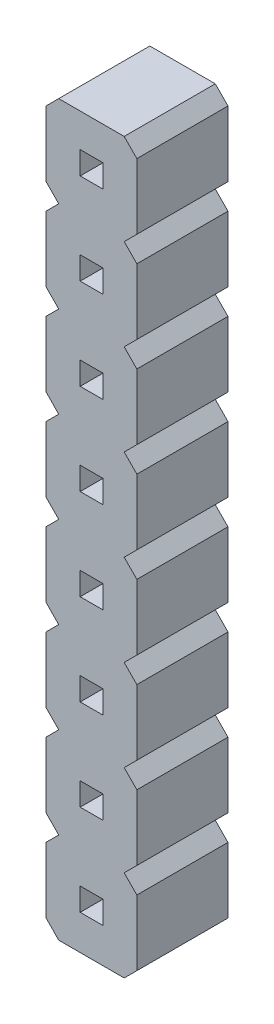
SolidWorks part; units mm, degrees
ref_plane "Alzado" through (0, 0, 0) normal (0, 0, 1) x (1, 0, 0)
ref_plane "Planta" through (0, 0, 0) normal (0, 1, 0) x (1, 0, 0)
ref_plane "Vista lateral" through (0, 0, 0) normal (1, 0, 0) x (0, 0, -1)
sketch "pin_drawing" plane through (0, 0, 0) normal (0, 0, 1) x (1, 0, 0)
  line L0 (0.9381, -1.0393) -> (-0.0144, -1.0393) construction
  line L1 (-0.0144, 2.0791) -> (-0.0144, 0.2531)
  line L2 (-0.0144, -0.4609) -> (-0.0144, -2.2869)
  line L3 (-0.0144, -0.4609) -> (0.3392, -0.1073)
  line L4 (1.5741, -1.6753) -> (2.5183, -1.6753) construction
  line L5 (-0.0144, 2.0791) -> (0.3392, 2.4327)
  line L6 (2.5183, -0.4665) -> (2.5183, -2.2938)
  line L7 (0.9381, -1.3573) -> (0.9381, -1.0393) construction
  line L8 (2.5183, -2.2938) -> (2.1647, -2.6473)
  line L9 (2.1647, -0.1073) -> (2.5183, -0.4665)
  line L10 (1.5741, -1.3573) -> (1.5741, -1.6753) construction
  line L11 (0.3392, -2.6473) -> (-0.0144, -2.2869)
  line L12 (0.9381, -1.0393) -> (1.5741, -1.0393)
  line L13 (0.9381, -1.0393) -> (0.9381, -1.6753)
  line L14 (0.9381, -1.6753) -> (1.5741, -1.6753)
  line L15 (1.5741, -1.0393) -> (1.5741, -1.6753)
  line L16 (2.5183, 2.0735) -> (2.5183, 0.2462)
  line L17 (2.5183, 0.2462) -> (2.1647, -0.1073)
  line L18 (2.1647, 2.4327) -> (2.5183, 2.0735)
  line L19 (0.3392, -0.1073) -> (-0.0144, 0.2531)
  line L20 (0.9381, 1.5007) -> (1.5741, 1.5007)
  line L21 (0.9381, 1.5007) -> (0.9381, 0.8647)
  line L22 (0.9381, 0.8647) -> (1.5741, 0.8647)
  line L23 (1.5741, 1.5007) -> (1.5741, 0.8647)
  line L24 (0.9381, 1.5007) -> (-0.0144, 1.5007) construction
  line L25 (1.5741, 0.8647) -> (2.5183, 0.8647) construction
  line L26 (0.9381, 1.1827) -> (0.9381, 1.5007) construction
  line L27 (1.5741, 1.1827) -> (1.5741, 0.8647) construction
  line L28 (-0.0144, 4.6191) -> (-0.0144, 2.7931)
  line L29 (-0.0144, 4.6191) -> (0.3392, 4.9727)
  line L30 (2.5183, 4.6135) -> (2.5183, 2.7862)
  line L31 (2.5183, 2.7862) -> (2.1647, 2.4327)
  line L32 (2.1647, 4.9727) -> (2.5183, 4.6135)
  line L33 (0.3392, 2.4327) -> (-0.0144, 2.7931)
  line L34 (0.9381, 4.0407) -> (1.5741, 4.0407)
  line L35 (0.9381, 4.0407) -> (0.9381, 3.4047)
  line L36 (0.9381, 3.4047) -> (1.5741, 3.4047)
  line L37 (1.5741, 4.0407) -> (1.5741, 3.4047)
  line L38 (0.9381, 4.0407) -> (-0.0144, 4.0407) construction
  line L39 (1.5741, 3.4047) -> (2.5183, 3.4047) construction
  line L40 (0.9381, 3.7227) -> (0.9381, 4.0407) construction
  line L41 (1.5741, 3.7227) -> (1.5741, 3.4047) construction
  line L42 (-0.0144, 7.1591) -> (-0.0144, 5.3331)
  line L43 (-0.0144, 7.1591) -> (0.3392, 7.5127)
  line L44 (2.5183, 7.1535) -> (2.5183, 5.3262)
  line L45 (2.5183, 5.3262) -> (2.1647, 4.9727)
  line L46 (2.1647, 7.5127) -> (2.5183, 7.1535)
  line L47 (0.3392, 4.9727) -> (-0.0144, 5.3331)
  line L48 (0.9381, 6.5807) -> (1.5741, 6.5807)
  line L49 (0.9381, 6.5807) -> (0.9381, 5.9447)
  line L50 (0.9381, 5.9447) -> (1.5741, 5.9447)
  line L51 (1.5741, 6.5807) -> (1.5741, 5.9447)
  line L52 (0.9381, 6.5807) -> (-0.0144, 6.5807) construction
  line L53 (1.5741, 5.9447) -> (2.5183, 5.9447) construction
  line L54 (0.9381, 6.2627) -> (0.9381, 6.5807) construction
  line L55 (1.5741, 6.2627) -> (1.5741, 5.9447) construction
  line L56 (-0.0144, 9.6991) -> (-0.0144, 7.8731)
  line L57 (-0.0144, 9.6991) -> (0.3392, 10.0527)
  line L58 (2.5183, 9.6935) -> (2.5183, 7.8662)
  line L59 (2.5183, 7.8662) -> (2.1647, 7.5127)
  line L60 (2.1647, 10.0527) -> (2.5183, 9.6935)
  line L61 (0.3392, 7.5127) -> (-0.0144, 7.8731)
  line L62 (0.9381, 9.1207) -> (1.5741, 9.1207)
  line L63 (0.9381, 9.1207) -> (0.9381, 8.4847)
  line L64 (0.9381, 8.4847) -> (1.5741, 8.4847)
  line L65 (1.5741, 9.1207) -> (1.5741, 8.4847)
  line L66 (0.9381, 9.1207) -> (-0.0144, 9.1207) construction
  line L67 (1.5741, 8.4847) -> (2.5183, 8.4847) construction
  line L68 (0.9381, 8.8027) -> (0.9381, 9.1207) construction
  line L69 (1.5741, 8.8027) -> (1.5741, 8.4847) construction
  line L70 (-0.0144, 12.2391) -> (-0.0144, 10.4131)
  line L71 (-0.0144, 12.2391) -> (0.3392, 12.5927)
  line L72 (2.5183, 12.2335) -> (2.5183, 10.4062)
  line L73 (2.5183, 10.4062) -> (2.1647, 10.0527)
  line L74 (2.1647, 12.5927) -> (2.5183, 12.2335)
  line L75 (0.3392, 10.0527) -> (-0.0144, 10.4131)
  line L76 (0.9381, 11.6607) -> (1.5741, 11.6607)
  line L77 (0.9381, 11.6607) -> (0.9381, 11.0247)
  line L78 (0.9381, 11.0247) -> (1.5741, 11.0247)
  line L79 (1.5741, 11.6607) -> (1.5741, 11.0247)
  line L80 (0.9381, 11.6607) -> (-0.0144, 11.6607) construction
  line L81 (1.5741, 11.0247) -> (2.5183, 11.0247) construction
  line L82 (0.9381, 11.3427) -> (0.9381, 11.6607) construction
  line L83 (1.5741, 11.3427) -> (1.5741, 11.0247) construction
  line L84 (-0.0144, 14.7791) -> (-0.0144, 12.9531)
  line L85 (-0.0144, 14.7791) -> (0.3392, 15.1327)
  line L86 (2.5183, 14.7735) -> (2.5183, 12.9462)
  line L87 (2.5183, 12.9462) -> (2.1647, 12.5927)
  line L88 (2.1647, 15.1327) -> (2.5183, 14.7735)
  line L89 (0.3392, 12.5927) -> (-0.0144, 12.9531)
  line L90 (0.9381, 14.2007) -> (1.5741, 14.2007)
  line L91 (0.9381, 14.2007) -> (0.9381, 13.5647)
  line L92 (0.9381, 13.5647) -> (1.5741, 13.5647)
  line L93 (1.5741, 14.2007) -> (1.5741, 13.5647)
  line L94 (0.9381, 14.2007) -> (-0.0144, 14.2007) construction
  line L95 (1.5741, 13.5647) -> (2.5183, 13.5647) construction
  line L96 (0.9381, 13.8827) -> (0.9381, 14.2007) construction
  line L97 (1.5741, 13.8827) -> (1.5741, 13.5647) construction
  line L98 (-0.0144, 17.3191) -> (-0.0144, 15.4931)
  line L99 (-0.0144, 17.3191) -> (0.3392, 17.6727)
  line L100 (2.5183, 17.3135) -> (2.5183, 15.4862)
  line L101 (2.5183, 15.4862) -> (2.1647, 15.1327)
  line L102 (2.1647, 17.6727) -> (2.5183, 17.3135)
  line L103 (0.3392, 15.1327) -> (-0.0144, 15.4931)
  line L104 (0.9381, 16.7407) -> (1.5741, 16.7407)
  line L105 (0.9381, 16.7407) -> (0.9381, 16.1047)
  line L106 (0.9381, 16.1047) -> (1.5741, 16.1047)
  line L107 (1.5741, 16.7407) -> (1.5741, 16.1047)
  line L108 (0.9381, 16.7407) -> (-0.0144, 16.7407) construction
  line L109 (1.5741, 16.1047) -> (2.5183, 16.1047) construction
  line L110 (0.9381, 16.4227) -> (0.9381, 16.7407) construction
  line L111 (1.5741, 16.4227) -> (1.5741, 16.1047) construction
  line L168 (2.1647, -2.6473) -> (0.3392, -2.6473)
  line L170 (0.3392, 17.6727) -> (2.1647, 17.6727)
  line L172 (0.9381, 18.9627) -> (0.9381, 19.2807) construction
  line L173 (0.9381, 19.2807) -> (0.9381, 18.6447) [skipped]
  line L174 (2.5183, 18.0262) -> (2.1647, 17.6727) [skipped]
  line L175 (0.3392, 17.6727) -> (-0.0144, 18.0331) [skipped]
  line L176 (0.9381, 18.6447) -> (1.5741, 18.6447) [skipped]
  line L177 (1.5741, 18.9627) -> (1.5741, 18.6447) [skipped]
  line L178 (1.5741, 18.9627) -> (1.5741, 18.6447) construction
  line L179 (1.5741, 18.6447) -> (2.5183, 18.6447) construction
  line L180 (2.5183, 18.6447) -> (2.5183, 18.0262) [skipped]
  line L181 (0.9381, 19.2807) -> (1.5741, 19.2807) [skipped]
  line L182 (0.9381, 19.2807) -> (-0.0144, 19.2807) construction
  line L183 (-0.0144, 19.8591) -> (-0.0144, 19.2807) [skipped]
  line L184 (-0.0144, 19.8591) -> (0.3392, 20.2127) [skipped]
  line L185 (0.3392, 20.2127) -> (-0.0144, 20.5731) [skipped]
  line L186 (2.5183, 20.5662) -> (2.1647, 20.2127) [skipped]
  line L187 (2.1647, 20.2127) -> (2.5183, 19.8535) [skipped]
  line L188 (0.9381, 21.5027) -> (0.9381, 21.8207) construction
  line L189 (2.5183, 22.3935) -> (2.5183, 21.1847) [skipped]
  line L190 (0.9381, 21.5027) -> (0.9381, 21.1847) [skipped]
  line L191 (0.9381, 21.1847) -> (1.5741, 21.1847) [skipped]
  line L192 (0.9381, 21.8207) -> (1.5741, 21.8207) [skipped]
  line L193 (1.5741, 21.5027) -> (1.5741, 21.1847) [skipped]
  line L194 (1.5741, 21.5027) -> (1.5741, 21.1847) construction
  line L195 (1.5741, 21.1847) -> (2.5183, 21.1847) construction
  line L196 (0.9381, 26.9007) -> (-0.0144, 26.9007) construction
  line L197 (-0.0144, 27.4791) -> (-0.0144, 25.6531) [skipped]
  line L198 (0.9381, 24.3607) -> (-0.0144, 24.3607) construction
  line L199 (-0.0144, 24.9391) -> (-0.0144, 23.1131) [skipped]
  line L200 (2.1647, 25.2927) -> (2.5183, 24.9335) [skipped]
  line L201 (1.5741, 24.0427) -> (1.5741, 23.7247) construction
  line L202 (0.9381, 23.7247) -> (1.5741, 23.7247) [skipped]
  line L203 (0.9381, 21.8207) -> (-0.0144, 21.8207) construction
  line L204 (-0.0144, 22.3991) -> (0.3392, 22.7527) [skipped]
  line L205 (0.3392, 22.7527) -> (-0.0144, 23.1131) [skipped]
  line L206 (-0.0144, 22.3991) -> (-0.0144, 21.8207) [skipped]
  line L207 (2.1647, 22.7527) -> (2.5183, 22.3935) [skipped]
  line L208 (2.5183, 23.7247) -> (2.5183, 23.1062) [skipped]
  line L209 (1.5741, 23.7247) -> (2.5183, 23.7247) construction
  line L210 (2.5183, 23.1062) -> (2.1647, 22.7527) [skipped]
  line L211 (0.9381, 24.3607) -> (1.5741, 24.3607) [skipped]
  line L212 (1.5741, 24.3607) -> (1.5741, 24.0427) [skipped]
  line L213 (0.9381, 24.3607) -> (0.9381, 24.0427) [skipped]
  line L214 (0.9381, 24.0427) -> (0.9381, 24.3607) construction
  line L215 (-0.0144, 24.9391) -> (0.3392, 25.2927) [skipped]
  line L216 (0.3392, 25.2927) -> (-0.0144, 25.6531) [skipped]
  line L217 (0.9381, 26.5827) -> (0.9381, 26.9007) construction
  line L218 (0.9381, 26.9007) -> (1.5741, 26.9007) [skipped]
  line L219 (0.9381, 26.2647) -> (1.5741, 26.2647) [skipped]
  line L220 (1.5741, 26.2647) -> (2.5183, 26.2647) construction
  line L221 (0.9381, 26.5827) -> (0.9381, 26.2647) [skipped]
  line L222 (1.5741, 26.5827) -> (1.5741, 26.2647) [skipped]
  line L223 (1.5741, 26.5827) -> (1.5741, 26.2647) construction
  line L224 (2.5183, 25.6462) -> (2.1647, 25.2927) [skipped]
  line L225 (2.1647, 27.8327) -> (2.5183, 27.4735) [skipped]
  line L226 (2.5183, 26.2647) -> (2.5183, 25.6462) [skipped]
  line L227 (-0.0144, 27.4791) -> (0.3392, 27.8327) [skipped]
  dimension "D1" = 0.318
  dimension "D2" = 0.9525
  dimension "D3" = 0.5
  dimension "D4" = 135
  dimension "D5" = 0.5
  dimension "D6" = 135
  dimension "D7" = 12
  dimension "D8" = 2.54
extrude "Boss-Extrude1" add sketch "pin_drawing" along normal blind 2.54
